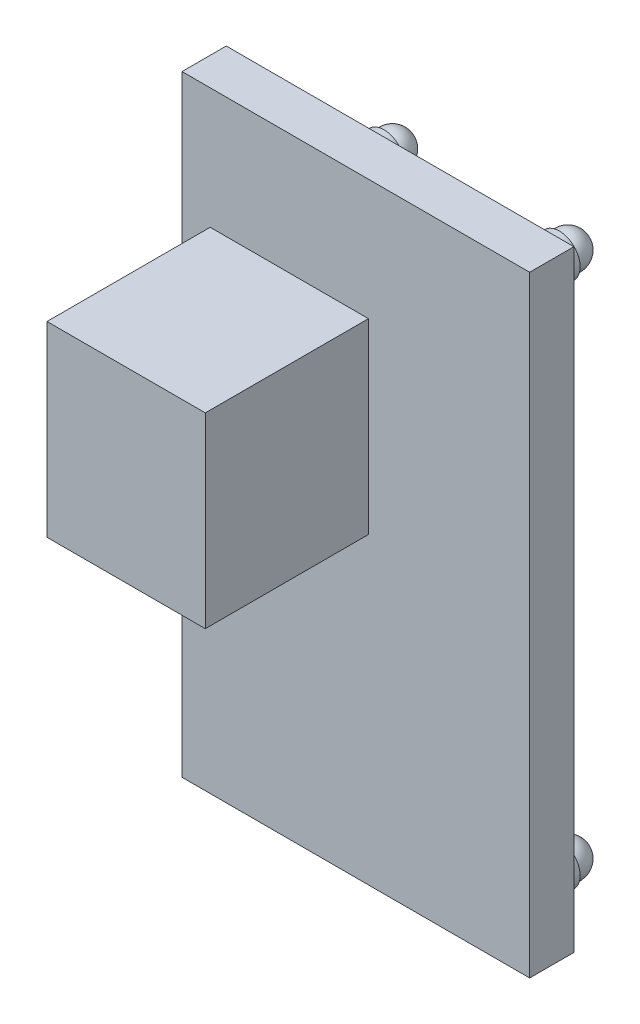
SolidWorks part; units mm, degrees
ref_plane "Front Plane" through (0, 0, 0) normal (0, 0, 1) x (1, 0, 0)
ref_plane "Top Plane" through (0, 0, 0) normal (0, 1, 0) x (1, 0, 0)
ref_plane "Right Plane" through (0, 0, 0) normal (1, 0, 0) x (0, 0, -1)
sketch "Sketch1" plane through (0, 0, 0) normal (0, 0, 1) x (1, 0, 0)
  line L1 (-6.285, -11.05) -> (6.285, -11.05)
  line L2 (-6.285, -11.05) -> (-6.285, 11.05)
  line L3 (-6.285, 11.05) -> (6.285, 11.05)
  line L4 (6.285, -11.05) -> (6.285, 11.05)
  line L5 (0, 11.05) -> (0, -11.05) construction
  line L6 (-6.285, 0) -> (6.285, 0) construction
  point P0 (0, 0)
  dimension "D1" = 12.57
  dimension "D2" = 22.1
extrude "Boss-Extrude1" add sketch "Sketch1" along normal blind 1.6 from offset 2
sketch "Sketch2" plane through (0, 0, 3.6) normal (0, 0, 1) x (1, 0, 0)
  line L1 (-5.2669, 6.6826) -> (0.4567, 6.6826)
  line L2 (-5.2669, 6.6826) -> (-5.2669, -0.0761)
  line L3 (-5.2669, -0.0761) -> (0.4567, -0.0761)
  line L4 (0.4567, 6.6826) -> (0.4567, -0.0761)
  line L5 (-2.4051, -0.0761) -> (-2.4051, 6.6826) construction
  line L6 (-5.2669, 3.3033) -> (0.4567, 3.3033) construction
  point P0 (-2.4051, 3.3033)
  point P4 (-2.8922, 5.2213)
  point P5 (-2.8314, 4.5819)
  point P6 (0.7916, 3.3033)
extrude "Boss-Extrude2" add sketch "Sketch2" along normal blind 5.9
sketch "Sketch3" plane through (0, 0, 2) normal (0, 0, -1) x (-1, 0, 0)
  line L1 (4.76, -9.53) -> (-4.76, -9.53) construction
  line L2 (4.76, -9.53) -> (4.76, 9.53) construction
  line L3 (4.76, 9.53) -> (-4.76, 9.53) construction
  line L4 (-4.76, -9.53) -> (-4.76, 9.53) construction
  line L5 (0, 9.53) -> (0, -9.53) construction
  line L6 (4.76, 0) -> (-4.76, 0) construction
  circle A0 centre (-4.76, 9.53) radius 0.75
  circle A2 centre (-4.76, -9.53) radius 0.75
  circle A3 centre (4.76, -9.53) radius 0.75
  circle A4 centre (1.58, 9.53) radius 0.75
  point P0 (0.794, 9.53)
  point P4 (0, 0)
  point P8 (-4.5667, 9.53)
  dimension "D3" = 1.5
  dimension "D5" = 1.5
  dimension "D6" = 1.5
  dimension "D7" = 1.5
  dimension "D1" = 19.06
  dimension "D2" = 9.52
  dimension "D4" = 6.34
extrude "Boss-Extrude3" add sketch "Sketch3" along normal blind 1
ref_plane "Plane1" through (0, 9.53, 0) normal (0, 1, 0) x (1, 0, 0)
sketch "Sketch4" plane through (0, 9.53, 0) normal (0, 1, 0) x (1, 0, 0)
  line L0 (5.51, -1) -> (4.01, -1) construction
  line L1 (4.76, -1.35) -> (4.76, -0.05)
  arc A0 (4.76, -0.05) -> (4.76, -1.35) centre (4.76, -0.7) ccw
  dimension "D1" = 1.3
  dimension "D2" = 0.3
revolve "Revolve1" add sketch "Sketch4" angle 360 about L1
sketch "Sketch5" plane through (0, 0, 1) normal (0, 0, -1) x (-1, 0, 0)
  point P0 (1.58, 9.53)
  point P1 (-4.76, -9.53)
  point P3 (4.76, -9.53)
pattern_sketch "Sketch-Pattern2" of "Revolve1"
